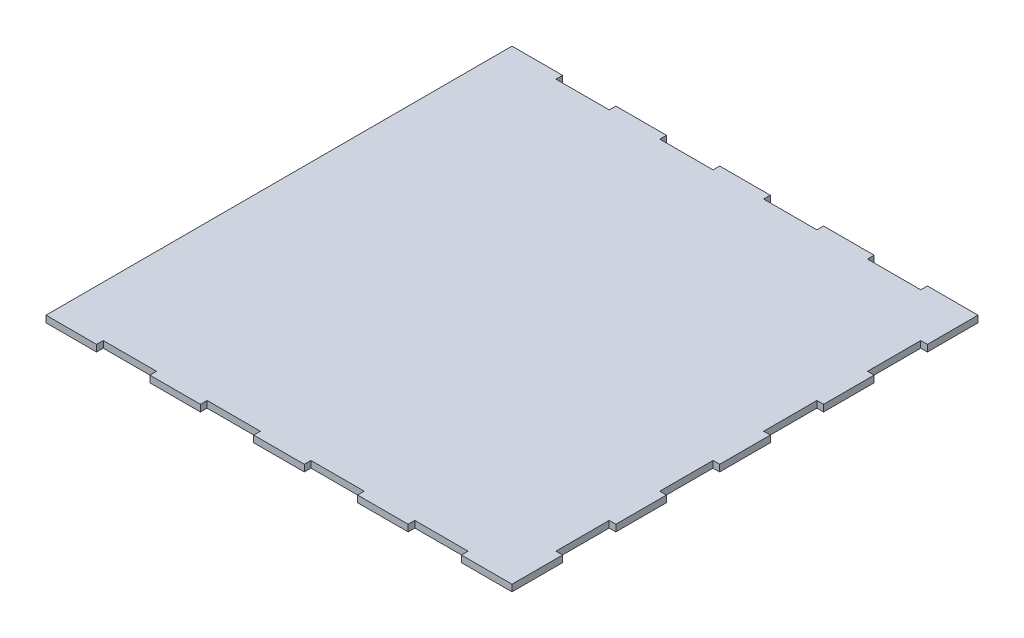
SolidWorks part; units mm, degrees
ref_plane "Front" through (0, 0, 0) normal (0, 0, 1) x (1, 0, 0)
ref_plane "Top" through (0, 0, 0) normal (0, 1, 0) x (1, 0, 0)
ref_plane "Right" through (0, 0, 0) normal (1, 0, 0) x (0, 0, -1)
sketch "Skizze1" plane through (0, 0, 0) normal (0, 1, 0) x (1, 0, 0)
  line L1 (175, 175) -> (-175, 175)
  line L2 (175, 175) -> (175, -175)
  line L3 (175, -175) -> (-175, -175)
  line L4 (-175, 175) -> (-175, -175)
  line L5 (175, 175) -> (-175, -175) construction
  line L6 (175, -175) -> (-175, 175) construction
  point P0 (0, 0)
  dimension "D1" = 350
  dimension "D2" = 350
extrude "Grundplatte" add sketch "Skizze1" along normal blind 5
ref_plane "Ebene1" through (0, 0, 0) normal (0, 0, 1) x (1, 0, 0)
ref_plane "Ebene2" through (0, 0, 0) normal (-1, 0, 0) x (0, 0, 1)
sketch "Skizze2" plane through (0, 5, 0) normal (0, 1, 0) x (1, 0, 0)
  line L0 (-175, 175) -> (-175, -175) construction
  line L5 (0, 175) -> (0, 0) construction
  line L6 (175, 175) -> (-175, 175) construction
  line L7 (137, 170) -> (175, 170) construction
  line L8 (19, 170) -> (-19, 170) construction
  line L13 (-137, 175) -> (-97, 175)
  line L14 (-137, 175) -> (-137, 170)
  line L15 (-137, 170) -> (-97, 170)
  line L16 (-97, 175) -> (-97, 170)
  line L17 (-59, 175) -> (-19, 175)
  line L18 (-59, 175) -> (-59, 170)
  line L19 (-59, 170) -> (-19, 170)
  line L20 (-19, 175) -> (-19, 170)
  line L21 (-59, 170) -> (-97, 170) construction
  line L22 (-137, 170) -> (-175, 170) construction
  line L23 (59, 170) -> (97, 170) construction
  line L24 (19, 175) -> (19, 170)
  line L25 (59, 170) -> (19, 170)
  line L42 (59, 175) -> (59, 170)
  line L43 (59, 175) -> (19, 175)
  line L44 (97, 175) -> (97, 170)
  line L45 (137, 170) -> (97, 170)
  line L46 (137, 175) -> (137, 170)
  line L63 (137, 175) -> (97, 175)
  point P12 (0, 170)
  dimension "D1" = 40
  dimension "D2" = 5
  dimension "D3" = 38
extrude "Schnitt-Linear austragen1" cut sketch "Skizze2" against normal through all
mirror "Spiegeln1" about plane through (0, 0, 0) normal (0, 0, 1) of "Schnitt-Linear austragen1"
ref_axis "Achse1" through (0, 10.2665, 0) along (0, -1, 0)
pattern_circular "Kreismuster1" count 2 over 90 about axis through (0, 0, 0) along (0, 1, 0) of "Schnitt-Linear austragen1"
